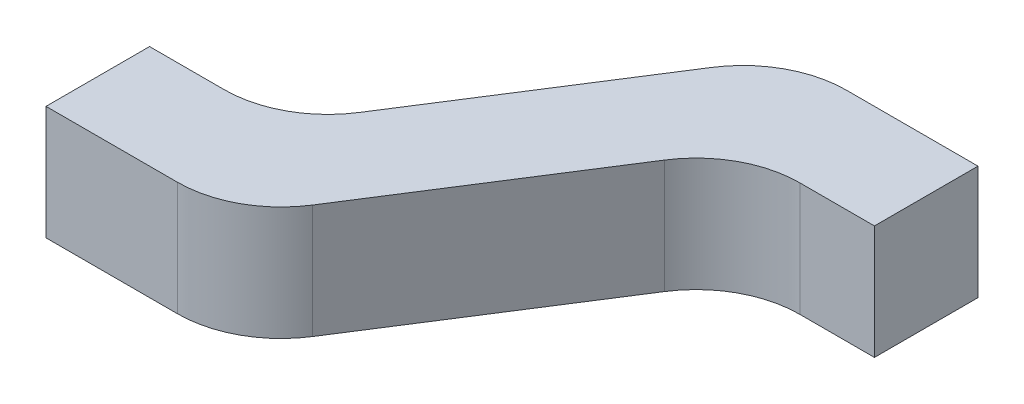
SolidWorks part; units mm, degrees
ref_plane "Front Plane" through (0, 0, 0) normal (0, 0, 1) x (1, 0, 0)
ref_plane "Top Plane" through (0, 0, 0) normal (0, 1, 0) x (1, 0, 0)
ref_plane "Right Plane" through (0, 0, 0) normal (1, 0, 0) x (0, 0, -1)
sketch "Sketch1" plane through (0, 0, 0) normal (0, 1, 0) x (1, 0, 0)
  line L0 (0, 0) -> (0.3088, 0) construction
  line L1 (0.3088, 0) -> (0.6912, 0.6) construction
  line L2 (0.6912, 0.6) -> (1, 0.6) construction
  line L3 (0, -0.1) -> (0.2539, -0.1)
  line L4 (0.4226, -0.0075) -> (0.6871, 0.4075)
  line L5 (0.8558, 0.5) -> (1, 0.5)
  line L6 (0, 0.1) -> (0.1442, 0.1)
  line L7 (0.3129, 0.1925) -> (0.5774, 0.6075)
  line L8 (0.7461, 0.7) -> (1, 0.7)
  line L9 (0, -0.1) -> (0, 0.1)
  line L10 (1, 0.5) -> (1, 0.7)
  line L11 (0, -0.1) -> (0.3636, -0.1) construction
  line L12 (0.3636, -0.1) -> (0.7461, 0.5) construction
  line L13 (0.7461, 0.5) -> (1, 0.5) construction
  line L14 (0.2539, 0.1) -> (0.6364, 0.7) construction
  line L15 (0.6364, 0.7) -> (1, 0.7) construction
  line L16 (0, 0.1) -> (0.2539, 0.1) construction
  arc A0 (0.2539, -0.1) -> (0.4226, -0.0075) centre (0.2539, 0.1) ccw
  arc A1 (0.6871, 0.4075) -> (0.8558, 0.5) centre (0.8558, 0.3) cw
  arc A2 (0.5774, 0.6075) -> (0.7461, 0.7) centre (0.7461, 0.5) cw
  arc A3 (0.1442, 0.1) -> (0.3129, 0.1925) centre (0.1442, 0.3) ccw
  dimension "D5" = 0.2
  dimension "D1" = 1
  dimension "D2" = 0.6
  dimension "D3" = 0.1
  dimension "D4" = 0.1
extrude "Boss-Extrude1" add sketch "Sketch1" along normal mid plane 0.22
